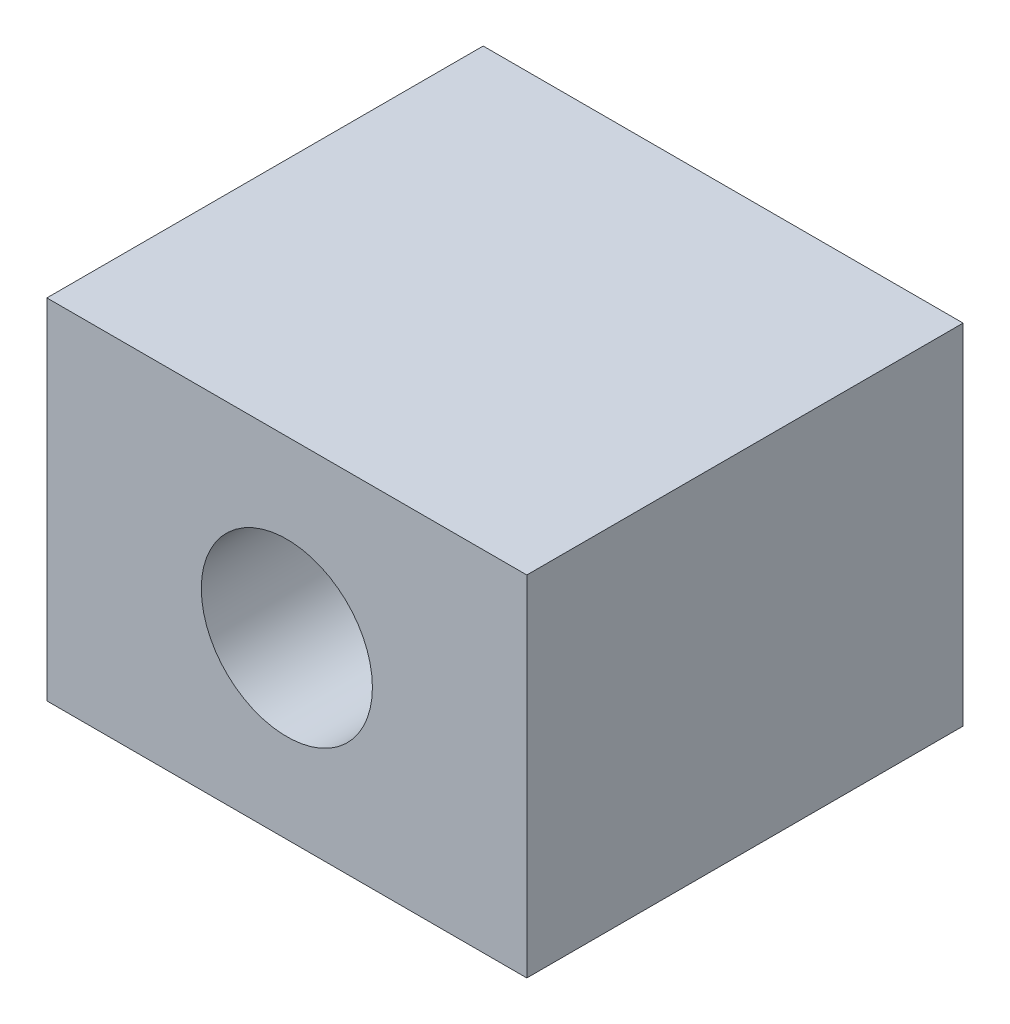
SolidWorks part; units mm, degrees
ref_plane "Plan de face" through (0, 0, 0) normal (0, 0, 1) x (1, 0, 0)
ref_plane "Plan de dessus" through (0, 0, 0) normal (0, 1, 0) x (1, 0, 0)
ref_plane "Plan de droite" through (0, 0, 0) normal (1, 0, 0) x (0, 0, -1)
sketch "Esquisse1" plane through (0, 0, 0) normal (0, 0, 1) x (1, 0, 0)
  line L1 (0, 0) -> (55, 0)
  line L2 (0, 0) -> (0, 40)
  line L3 (0, 40) -> (55, 40)
  line L4 (55, 0) -> (55, 40)
  dimension "D1" = 40
  dimension "D2" = 55
extrude "Boss.-Extru.1" add sketch "Esquisse1" along normal blind 50
sketch "Esquisse2" plane through (0, 0, 50) normal (0, 0, 1) x (1, 0, 0)
  line L0 (27.5, 40) -> (27.5, 0) construction
  line L1 (55, 40) -> (0, 40) construction
  line L2 (0, 0) -> (55, 0) construction
  line L3 (0, 20) -> (55, 20) construction
  line L6 (0, 40) -> (0, 0) construction
  line L7 (55, 0) -> (55, 40) construction
  circle A0 centre (27.5, 20) radius 9.8049
extrude "Enlèv. mat.-Extru.1" cut sketch "Esquisse2" against normal blind 100
